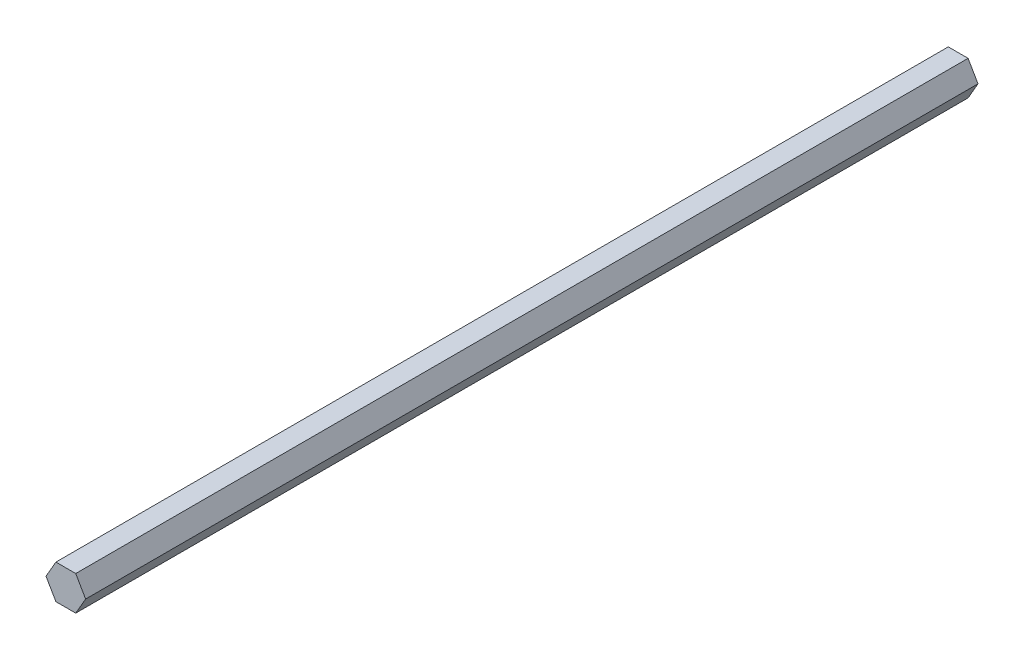
SolidWorks part; units mm, degrees
material "1060 Alloy"
ref_plane "Front Plane" through (0, 0, 0) normal (0, 0, 1) x (1, 0, 0)
ref_plane "Top Plane" through (0, 0, 0) normal (0, 1, 0) x (1, 0, 0)
ref_plane "Right Plane" through (0, 0, 0) normal (1, 0, 0) x (0, 0, -1)
sketch "Sketch1" plane through (0, 0, 0) normal (0, 0, 1) x (1, 0, 0)
  line L1 (-3.6662, 6.35) -> (-7.3323, 0)
  line L2 (-7.3323, 0) -> (-3.6662, -6.35)
  line L3 (-3.6662, -6.35) -> (3.6662, -6.35)
  line L4 (3.6662, -6.35) -> (7.3323, 0)
  line L5 (7.3323, 0) -> (3.6662, 6.35)
  line L6 (3.6662, 6.35) -> (-3.6662, 6.35)
  circle A0 centre (0, 0) radius 6.35 construction
  circle A1 centre (0, 0) radius 6.35 construction
  dimension "D1" = 12.7
extrude "Boss-Extrude1" add sketch "Sketch1" along normal blind 330.2
